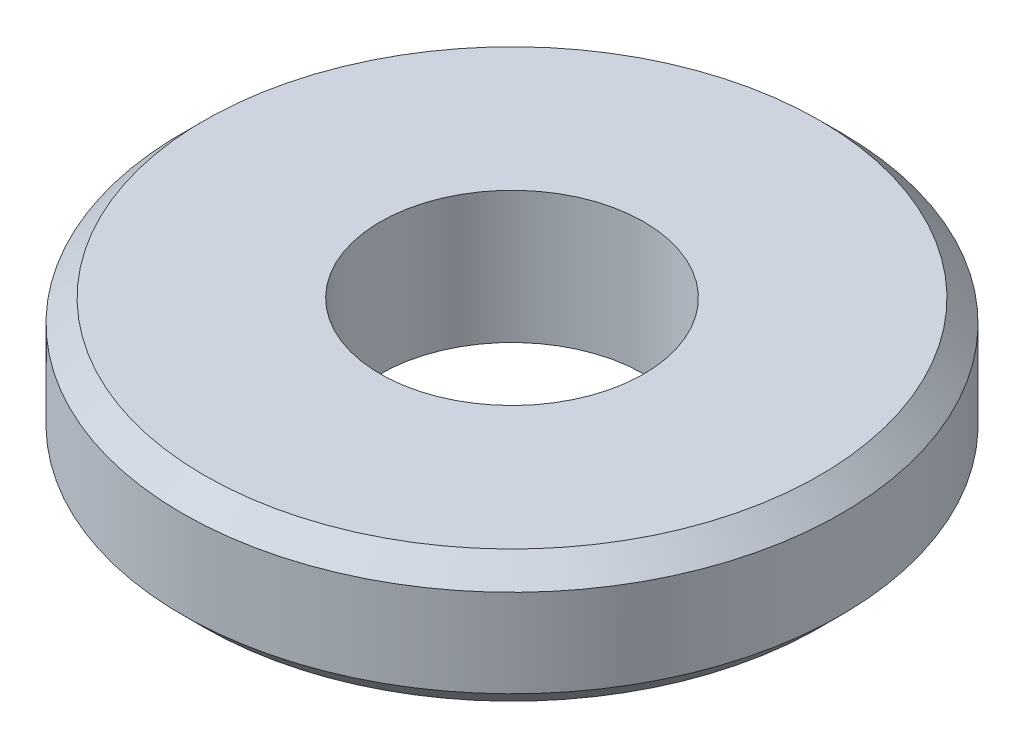
SolidWorks part; units mm, degrees
material "Сталь ШХ15 ГОСТ 801-78"
ref_plane "Plane1" through (0, 0, 0) normal (0, 0, 1) x (1, 0, 0)
ref_plane "Plane2" through (0, 0, 0) normal (0, 1, 0) x (1, 0, 0)
ref_plane "Plane3" through (0, 0, 0) normal (1, 0, 0) x (0, 0, -1)
sketch "Эскиз1" plane through (0, 0, 0) normal (0, 0, 1) x (1, 0, 0)
  line L6 (0, 0) -> (0, 6.4893) construction
  line L7 (6, 0) -> (6, 6)
  line L8 (6, 6) -> (15, 6)
  line L9 (15, 6) -> (15, 0)
  line L10 (15, 0) -> (6, 0)
  point P2 (3.3365, -0.354)
  point P5 (3.5, 0)
  dimension "D1" = 6
  dimension "D3" = 15
  dimension "D5" = 6
revolve "Повернуть1" add sketch "Эскиз1" angle 360 about L6
chamfer "Фаска4" distance 1 angle 45 2 edges at (0, 0, -15) (0, 6, -15)
